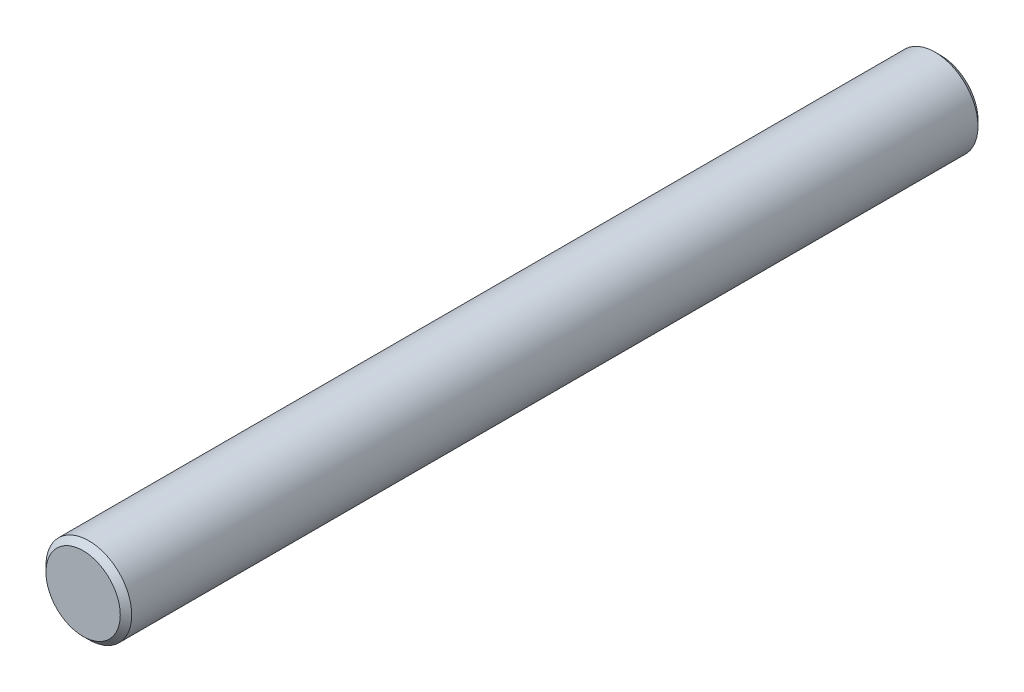
SolidWorks part; units mm, degrees
ref_plane "정면" through (0, 0, 0) normal (0, 0, 1) x (1, 0, 0)
ref_plane "윗면" through (0, 0, 0) normal (0, 1, 0) x (1, 0, 0)
ref_plane "우측면" through (0, 0, 0) normal (1, 0, 0) x (0, 0, -1)
sketch "스케치1" plane through (0, 0, 0) normal (0, 0, 1) x (1, 0, 0)
  circle A0 centre (0, 0) radius 1.5
  dimension "D1" = 3
extrude "보스-돌출1" add sketch "스케치1" along normal blind 30
chamfer "모따기1" distance 0.2 angle 45 2 edges at (1.5, 0, 0) (1.5, 0, 30)
